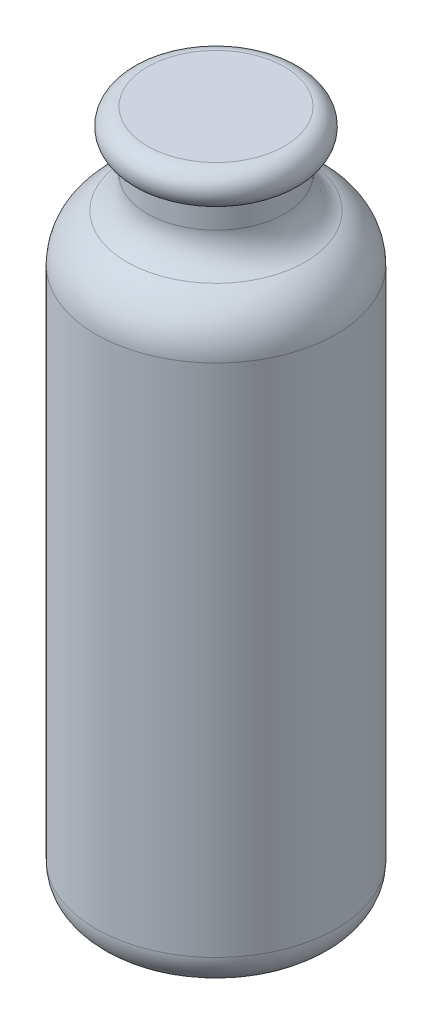
SolidWorks part; units mm, degrees
material "2014 Alloy"
ref_plane "Front Plane" through (0, 0, 0) normal (0, 0, 1) x (1, 0, 0)
ref_plane "Top Plane" through (0, 0, 0) normal (0, 1, 0) x (1, 0, 0)
ref_plane "Right Plane" through (0, 0, 0) normal (1, 0, 0) x (0, 0, -1)
sketch "Sketch1" plane through (0, 0, 0) normal (0, 0, 1) x (1, 0, 0)
  line L0 (0, 284.8767) -> (0, -145.2693) construction
  line L1 (-35, 10) -> (-35, 160)
  line L2 (-25, 0) -> (0, 0)
  line L3 (-20, 200) -> (0, 200)
  line L5 (-20, 190) -> (-20, 182.9129)
  line L23 (-25, 1) -> (0, 1)
  line L24 (-34, 10) -> (-34, 160)
  line L27 (0, 200) -> (0, 199)
  line L28 (0, 1) -> (0, 0)
  line L29 (5.4864, 191) -> (-46.3746, 191) construction
  line L30 (-19, 191.127) -> (-19, 182.9129) construction
  line L31 (-20, 199) -> (0, 199) construction
  line L32 (0, 199) -> (-20, 199)
  line L33 (-19, 182.9129) -> (-19, 191)
  line L34 (-20, 191) -> (-19, 191)
  arc A0 (-35, 160) -> (-26, 173.7477) centre (-20, 160) cw
  arc A2 (-20, 190) -> (-20, 200) centre (-20, 195) cw
  arc A3 (-20, 182.9129) -> (-26, 173.7477) centre (-30, 182.9129) cw
  arc A11 (-25, 0) -> (-35, 10) centre (-25, 10) cw
  arc A12 (-25, 1) -> (-34, 10) centre (-25, 10) cw
  arc A13 (-34, 160) -> (-25.6, 172.8312) centre (-20, 160) cw
  arc A14 (-19, 182.9129) -> (-25.6, 172.8312) centre (-30, 182.9129) cw
  arc A16 (-19, 191.127) -> (-20, 199) centre (-20, 195) cw construction
  arc A21 (-20, 190) -> (-20, 200) centre (-20, 195) cw construction
  arc A23 (-20, 191) -> (-20, 199) centre (-20, 195) cw
  point P34 (-35, 0)
  dimension "D3" = 5
  dimension "D4" = 15
  dimension "D5" = 10
  dimension "D8" = 10
  dimension "D1" = 70
  dimension "D2" = 160
  dimension "D6" = 200
  dimension "D7" = 1
revolve "Revolve2" add sketch "Sketch1" angle 360 about L0
